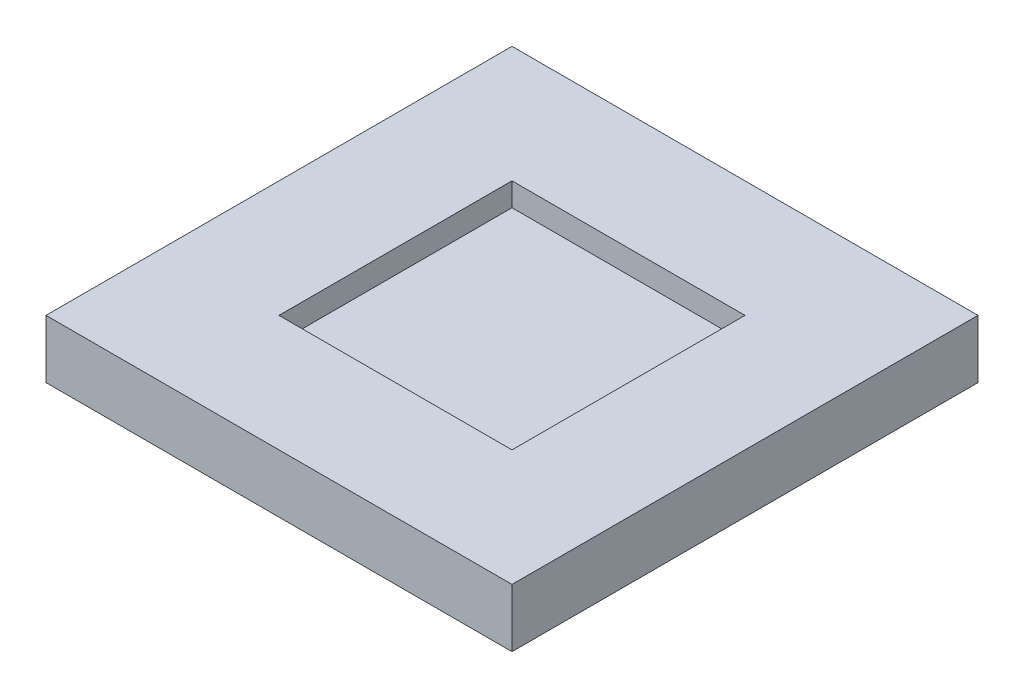
SolidWorks part; units mm, degrees
ref_plane "Front Plane" through (0, 0, 0) normal (0, 0, 1) x (1, 0, 0)
ref_plane "Top Plane" through (0, 0, 0) normal (0, 1, 0) x (1, 0, 0)
ref_plane "Right Plane" through (0, 0, 0) normal (1, 0, 0) x (0, 0, -1)
sketch "Sketch1" plane through (0, 0, 0) normal (0, 1, 0) x (1, 0, 0)
  line L1 (50.8, 50.8) -> (-50.8, 50.8)
  line L2 (50.8, 50.8) -> (50.8, -50.8)
  line L3 (50.8, -50.8) -> (-50.8, -50.8)
  line L4 (-50.8, 50.8) -> (-50.8, -50.8)
  line L5 (50.8, 50.8) -> (-50.8, -50.8) construction
  line L6 (50.8, -50.8) -> (-50.8, 50.8) construction
  point P0 (0, 0)
  dimension "D1" = 101.6
extrude "Boss-Extrude1" add sketch "Sketch1" along normal blind 12.7
sketch "Sketch2" plane through (0, 12.7, 0) normal (0, 1, 0) x (1, 0, 0)
  line L0 (-50.8, -50.8) -> (50.8, -50.8) construction
  line L1 (25.4, 25.4) -> (-25.4, 25.4)
  line L2 (25.4, 25.4) -> (25.4, -25.4)
  line L3 (25.4, -25.4) -> (-25.4, -25.4)
  line L4 (-25.4, 25.4) -> (-25.4, -25.4)
  line L5 (25.4, 25.4) -> (-25.4, -25.4) construction
  line L6 (25.4, -25.4) -> (-25.4, 25.4) construction
  point P0 (0, 0)
  dimension "D1" = 25.4
extrude "Cut-Extrude1" cut sketch "Sketch2" against normal blind 5.08
